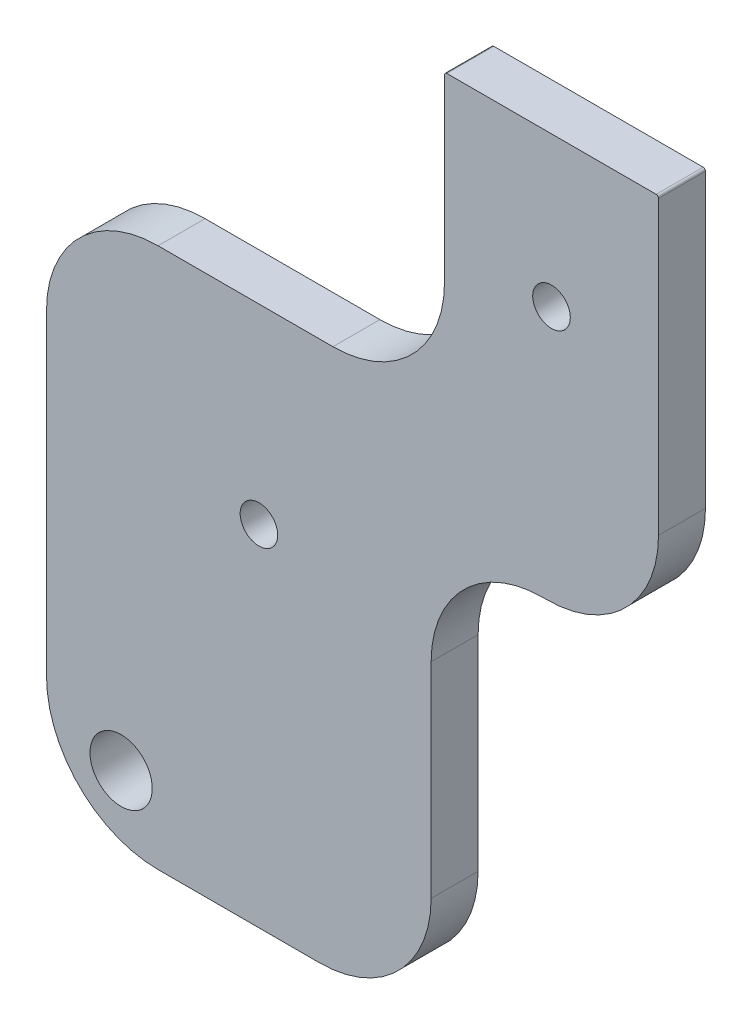
SolidWorks part; units mm, degrees
ref_plane "Front Plane" through (0, 0, 0) normal (0, 0, 1) x (1, 0, 0)
ref_plane "Top Plane" through (0, 0, 0) normal (0, 1, 0) x (1, 0, 0)
ref_plane "Right Plane" through (0, 0, 0) normal (1, 0, 0) x (0, 0, -1)
sketch "Sketch1" plane through (0, 0, 0) normal (0, 0, 1) x (1, 0, 0)
  line L1 (73.262, -348.9535) -> (106.0084, -348.9535)
  line L2 (73.262, -348.9535) -> (73.262, -302.9535)
  line L3 (107.1484, -277.9535) -> (125.3684, -277.9535)
  line L4 (125.3684, -312.5035) -> (125.3684, -277.9535)
  line L7 (125.3684, -312.5035) -> (106.0084, -312.5035)
  line L8 (106.0084, -348.9535) -> (106.0084, -312.5035)
  line L9 (73.262, -302.9535) -> (107.1484, -302.9535)
  line L10 (107.1484, -277.9535) -> (107.1484, -302.9535)
extrude "Boss-Extrude1" add sketch "Sketch1" against normal blind 4
fillet "Fillet1" radius 9.5 6 edges at (73.262, -348.9535, -2) (106.0084, -348.9535, -2) (125.3684, -312.5035, -2) (73.262, -302.9535, -2) (107.1484, -302.9535, -2) (106.0084, -312.5035, -2)
hole_wizard "M3 Clearance Hole1" positions "Sketch3" profile "Sketch2" hole size "M3" standard "ISO" end condition through all
sketch "Sketch3" plane through (0, 0, 0) normal (0, 0, 1) x (1, 0, 0)
  point P0 (116.2584, -290.7035)
  point P2 (91.3484, -319.2035)
sketch "Sketch2" plane through (116.2584, -290.7035, 0) normal (1, 0, 0) x (0, -1, 0)
  line L0 (0, 0) -> (0, 4)
  line L1 (0, 4) -> (1.6, 4)
  line L2 (1.6, 4) -> (1.6, 0)
  line L5 (1.6, 0) -> (0, 0)
  line L11 (0, -6.35) -> (0, 107.95) construction
  dimension "Thru Hole Dia." = 3.2
  dimension "Thru Hole Depth" = 4
hole_wizard "M5 Clearance Hole1" positions "Sketch5" profile "Sketch4" hole size "M5" standard "ISO" end condition through all
sketch "Sketch5" plane through (0, 0, 0) normal (0, 0, 1) x (1, 0, 0)
  point P0 (79.6121, -343.2233)
sketch "Sketch4" plane through (79.6121, -343.2233, 0) normal (1, 0, 0) x (0, -1, 0)
  line L0 (0, 0) -> (0, 4)
  line L1 (0, 4) -> (2.65, 4)
  line L2 (2.65, 4) -> (2.65, 0)
  line L5 (2.65, 0) -> (0, 0)
  line L11 (0, -6.35) -> (0, 107.95) construction
  dimension "Thru Hole Dia." = 5.3
  dimension "Thru Hole Depth" = 4
fillet "Fillet2" radius 0.2 2 edges at (125.3684, -277.9535, -2) (107.1484, -277.9535, -2)
